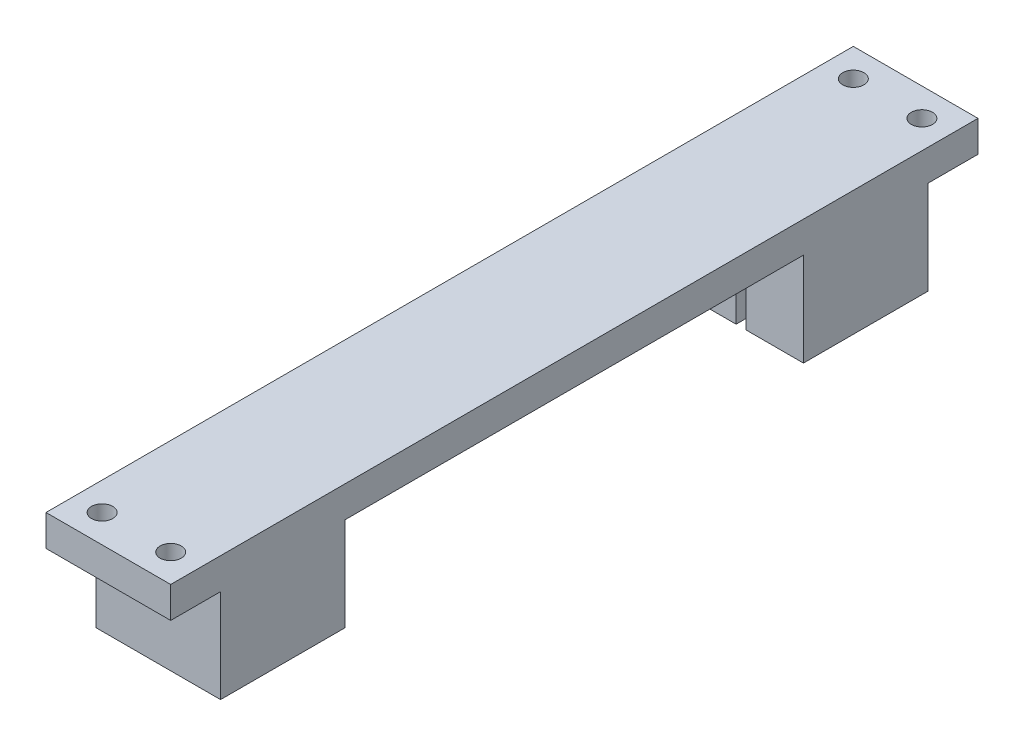
SolidWorks part; units mm, degrees
ref_plane "Front Plane" through (0, 0, 0) normal (0, 0, 1) x (1, 0, 0)
ref_plane "Top Plane" through (0, 0, 0) normal (0, 1, 0) x (1, 0, 0)
ref_plane "Right Plane" through (0, 0, 0) normal (1, 0, 0) x (0, 0, -1)
sketch "Sketch1" plane through (0, 0, 0) normal (0, 1, 0) x (1, 0, 0)
  line L1 (-10, -14) -> (10, -14)
  line L2 (-10, -14) -> (-10, 14)
  line L3 (-10, 14) -> (10, 14)
  line L4 (10, -14) -> (10, 14)
  line L5 (-10, -14) -> (10, 14) construction
  line L6 (-10, 14) -> (10, -14) construction
  point P0 (0, 0)
  dimension "D1" = 20
  dimension "D2" = 28
extrude "Boss-Extrude1" add sketch "Sketch1" along normal blind 5 contours L4 L3 L2 L1
sketch "Sketch2" plane through (0, 0, 0) normal (0, -1, 0) x (-1, 0, 0)
  line L0 (10, -14) -> (10, 14) construction
  line L1 (-10, 14) -> (10, 14)
  line L2 (-10, 14) -> (-10, -6)
  line L3 (-10, -6) -> (10, -6)
  line L4 (10, 14) -> (10, -6)
  dimension "D1" = 20
extrude "Boss-Extrude2" add sketch "Sketch2" along normal blind 15
sketch "Sketch3" plane through (0, -15, 0) normal (0, -1, 0) x (-1, 0, 0)
  line L0 (10, 14) -> (-10, 14) construction
  line L1 (-0.8, 14) -> (0.8, 14)
  line L2 (-0.8, 14) -> (-0.8, 6.5)
  line L3 (-0.8, 6.5) -> (0.8, 6.5)
  line L4 (0.8, 14) -> (0.8, 6.5)
  line L5 (-10, 14) -> (-10, -6) construction
  dimension "D1" = 1.6
  dimension "D2" = 7.5
  dimension "D3" = 9.2
extrude "Cut-Extrude1" cut sketch "Sketch3" against normal blind 15
hole_wizard "M3 Clearance Hole1" positions "Sketch5" profile "Sketch4" hole size "M3" standard "ANSI Metric"
sketch "Sketch5" plane through (0, 0, 0) normal (0, -1, 0) x (-1, 0, 0)
  line L0 (-10, -6) -> (10, -6) construction
  line L2 (-10, -14) -> (-10, -6) construction
  line L3 (10, -14) -> (10, -6) construction
  point P1 (-5.5, -9.5)
  point P3 (5.5, -9.5)
  dimension "D1" = 3.5
  dimension "D2" = 3.5
  dimension "D3" = 4.5
  dimension "D4" = 4.5
sketch "Sketch4" plane through (5.5, 0, 9.5) normal (1, 0, 0) x (0, 0, -1)
  line L0 (0, 0) -> (0, 6.0205)
  line L1 (0, 6.0205) -> (1.7, 4.999)
  line L2 (1.7, 4.999) -> (1.7, 0)
  line L5 (1.7, 0) -> (0, 0)
  line L10 (0, 6.0205) -> (-1.7, 4.999) construction
  line L11 (0, -6.35) -> (0, 107.95) construction
  dimension "Hole Dia." = 3.4
  dimension "Hole Depth" = 4.999
  dimension "Drill Angle" = 118
sketch "Sketch6" plane through (0, 0, -14) normal (0, 0, -1) x (-1, 0, 0)
  line L0 (-10, 5) -> (-10, -15) construction
  line L1 (10, 5) -> (-10, 5)
  line L2 (10, 5) -> (10, 0)
  line L3 (10, 0) -> (-10, 0)
  line L4 (-10, 5) -> (-10, 0)
extrude "Boss-Extrude3" add sketch "Sketch6" along normal blind 93.5
sketch "Sketch7" plane through (0, 0, -107.5) normal (0, 0, -1) x (-1, 0, 0)
  line L1 (-10, 5) -> (10, 5)
  line L2 (-10, 5) -> (-10, 0)
  line L3 (-10, 0) -> (10, 0)
  line L4 (10, 5) -> (10, 0)
extrude "Boss-Extrude4" add sketch "Sketch7" along normal blind 8
sketch "Sketch8" plane through (0, 0, 0) normal (0, -1, 0) x (-1, 0, 0)
  line L1 (-10, 115.5) -> (-10, 14) construction
  line L2 (-10, 87.5) -> (10, 87.5)
  line L3 (-10, 87.5) -> (-10, 107.5)
  line L5 (-10, 107.5) -> (10, 107.5)
  line L6 (10, 87.5) -> (10, 107.5)
  line L7 (10, 115.5) -> (10, 14) construction
  line L8 (-10, 115.5) -> (10, 115.5) construction
  dimension "D1" = 20
  dimension "D2" = 8
extrude "Boss-Extrude5" add sketch "Sketch8" along normal blind 15
sketch "Sketch9" plane through (0, -15, 0) normal (0, -1, 0) x (-1, 0, 0)
  line L1 (0.8, 60) -> (-0.8, 60)
  line L2 (0.8, 60) -> (0.8, 95.5)
  line L3 (0.8, 95.5) -> (-0.8, 95.5)
  line L4 (-0.8, 60) -> (-0.8, 95.5)
  line L9 (-10, 107.5) -> (-10, 87.5) construction
  line L10 (10, 107.5) -> (-10, 107.5) construction
  dimension "D1" = 1.6
  dimension "D2" = 9.2
  dimension "D3" = 12
extrude "Cut-Extrude2" cut sketch "Sketch9" against normal blind 15
hole_wizard "M3 Clearance Hole2" positions "Sketch11" profile "Sketch10" hole size "M3" standard "ANSI Metric" end condition through all
sketch "Sketch11" plane through (0, 0, 0) normal (0, -1, 0) x (-1, 0, 0)
  line L0 (10, 107.5) -> (-10, 107.5) construction
  line L1 (-10, 115.5) -> (-10, 107.5) construction
  line L2 (10, 115.5) -> (10, 107.5) construction
  point P0 (-5.5, 111)
  point P2 (5.5, 111)
  dimension "D1" = 3.5
  dimension "D2" = 3.5
  dimension "D3" = 4.5
  dimension "D4" = 4.5
sketch "Sketch10" plane through (5.5, 0, -111) normal (1, 0, 0) x (0, 0, -1)
  line L0 (0, 0) -> (0, 5)
  line L1 (0, 5) -> (1.7, 5)
  line L2 (1.7, 5) -> (1.7, 0)
  line L5 (1.7, 0) -> (0, 0)
  line L11 (0, -6.35) -> (0, 107.95) construction
  dimension "Thru Hole Dia." = 3.4
  dimension "Thru Hole Depth" = 5
